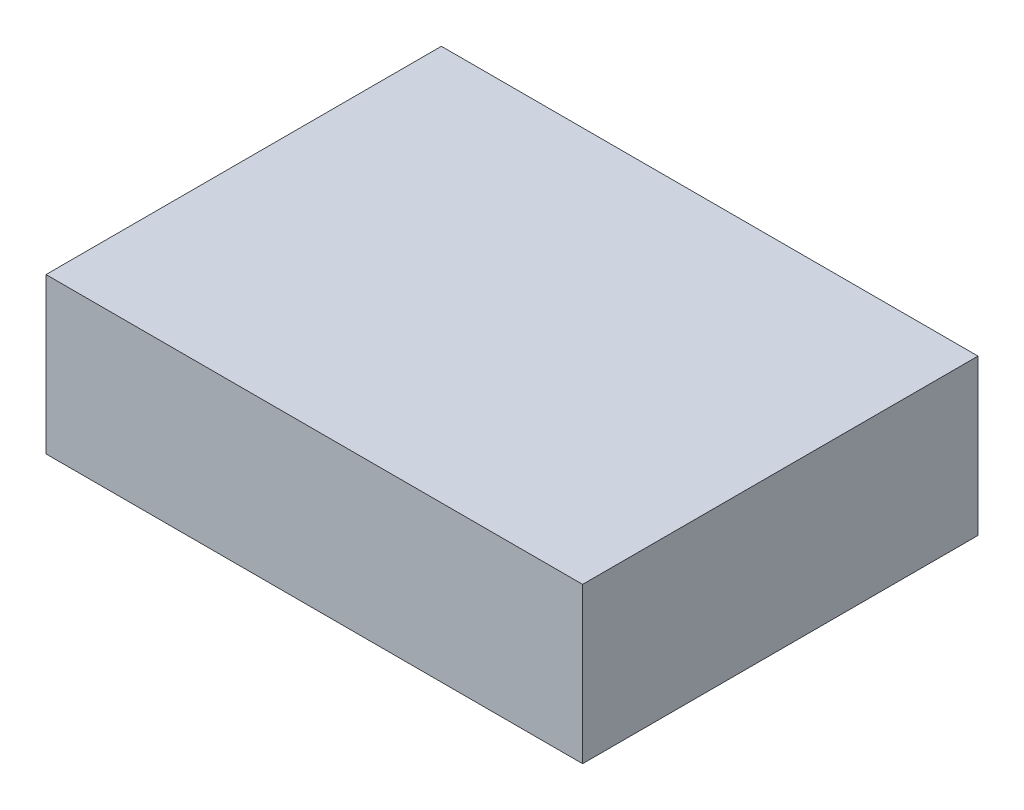
SolidWorks part; units mm, degrees
material "AISI 1020"
ref_plane "Спереди" through (0, 0, 0) normal (0, 0, 1) x (1, 0, 0)
ref_plane "Сверху" through (0, 0, 0) normal (0, 1, 0) x (1, 0, 0)
ref_plane "Справа" through (0, 0, 0) normal (1, 0, 0) x (0, 0, -1)
sketch "Эскиз1" plane through (0, 0, 0) normal (0, 1, 0) x (1, 0, 0)
  line L1 (-475, -350) -> (475, -350)
  line L2 (-475, -350) -> (-475, 350)
  line L3 (-475, 350) -> (475, 350)
  line L4 (475, -350) -> (475, 350)
  line L5 (-475, -350) -> (475, 350) construction
  line L6 (-475, 350) -> (475, -350) construction
  point P0 (0, 0)
  dimension "D1" = 950
  dimension "D2" = 700
extrude "Габарит ARM600" add sketch "Эскиз1" along normal blind 275
